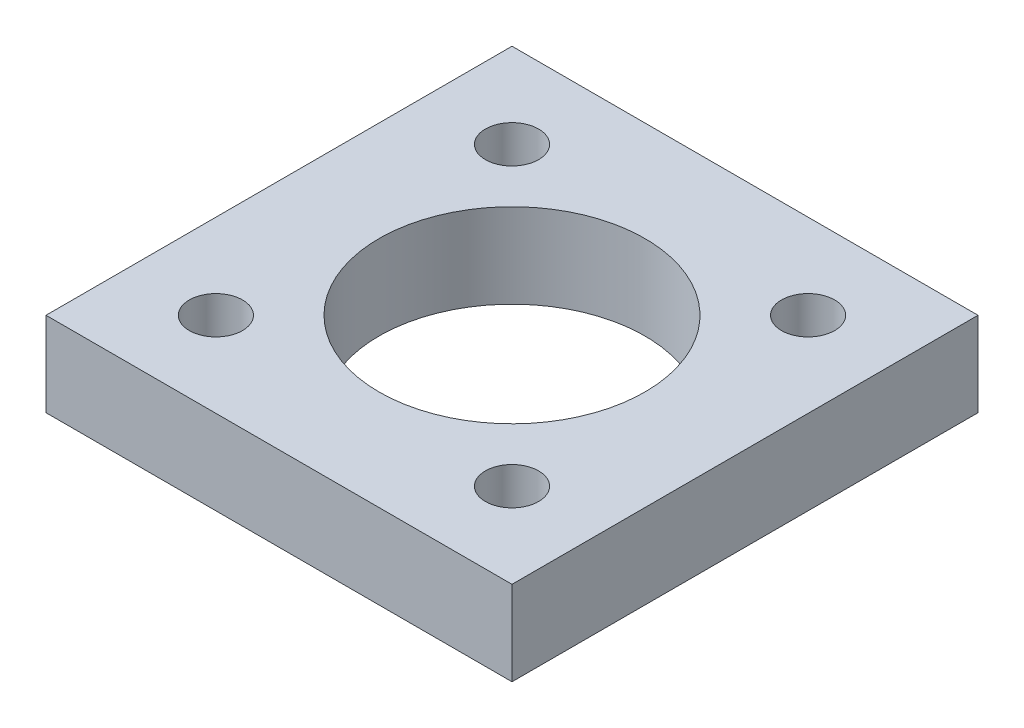
SolidWorks part; units mm, degrees
ref_plane "Front Plane" through (0, 0, 0) normal (0, 0, 1) x (1, 0, 0)
ref_plane "Top Plane" through (0, 0, 0) normal (0, 1, 0) x (1, 0, 0)
ref_plane "Right Plane" through (0, 0, 0) normal (1, 0, 0) x (0, 0, -1)
sketch "Sketch1" plane through (0, 0, 0) normal (0, 1, 0) x (1, 0, 0)
  line L1 (8.763, -8.763) -> (-8.763, -8.763)
  line L2 (8.763, -8.763) -> (8.763, 8.763)
  line L3 (8.763, 8.763) -> (-8.763, 8.763)
  line L4 (-8.763, -8.763) -> (-8.763, 8.763)
  line L5 (8.763, -8.763) -> (-8.763, 8.763) construction
  line L6 (8.763, 8.763) -> (-8.763, -8.763) construction
  circle A0 centre (-5.5678, 5.5678) radius 1
  circle A1 centre (5.5678, 5.5678) radius 1
  circle A2 centre (5.5678, -5.5678) radius 1
  circle A3 centre (-5.5678, -5.5678) radius 1
  circle A4 centre (0, 0) radius 5
  point P0 (0, 0)
  point P17 (0, 0)
  dimension "D2" = 7.874
  dimension "D3" = 2
  dimension "D5" = 10
  dimension "D1" = 17.526
  dimension "D4" = 4
extrude "Boss-Extrude1" add sketch "Sketch1" along normal blind 3.175
